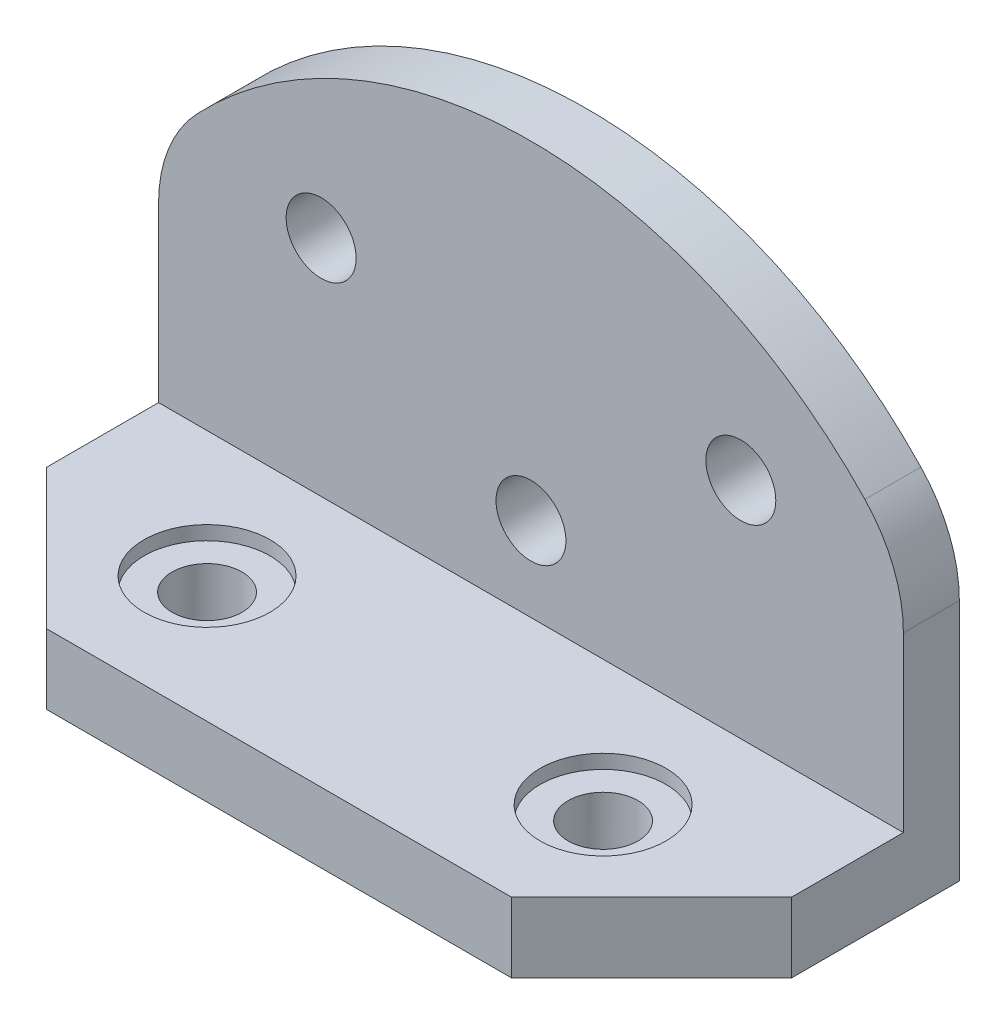
SolidWorks part; units mm, degrees
ref_plane "Front Plane" through (0, 0, 0) normal (0, 0, 1) x (1, 0, 0)
ref_plane "Top Plane" through (0, 0, 0) normal (0, 1, 0) x (1, 0, 0)
ref_plane "Right Plane" through (0, 0, 0) normal (1, 0, 0) x (0, 0, -1)
sketch "Sketch1" plane through (0, 0, 0) normal (0, 0, 1) x (1, 0, 0)
  line L0 (-7.5003, 10.7252) -> (7.4997, 10.7252) construction
  line L1 (-13.3097, 0.2252) -> (13.3097, 0.2252)
  line L2 (13.3097, 0.2252) -> (13.3097, 8.9074)
  line L3 (-13.3097, 8.9074) -> (-13.3097, 0.2252)
  line L4 (-0.0003, 5.7252) -> (-0.0003, 10.7252) construction
  arc A0 (13.3097, 8.9074) -> (11.935, 12.3509) centre (8.3097, 8.9074) ccw
  arc A1 (11.935, 12.3509) -> (-11.935, 12.3509) centre (0, 1.0143) ccw
  arc A2 (-11.935, 12.3509) -> (-13.3097, 8.9074) centre (-8.3097, 8.9074) ccw
  circle A3 centre (7.4997, 10.7252) radius 1.25
  circle A4 centre (-7.5003, 10.7252) radius 1.25
  circle A5 centre (-0.0003, 5.7252) radius 1.25
  dimension "D1" = 2.5
  dimension "D2" = 15
  dimension "D3" = 5
  dimension "D4" = 5.5
  dimension "D5" = 13.31
extrude "Boss-Extrude1" add sketch "Sketch1" along normal blind 2
sketch "Sketch2" plane through (0, 0, 2) normal (0, 0, 1) x (1, 0, 0)
  line L0 (13.3097, 0.2252) -> (13.3097, 8.9074) construction
  line L1 (-13.3097, 0.2252) -> (13.3097, 0.2252)
  line L2 (-13.3097, 0.2252) -> (-13.3097, 2.7252)
  line L3 (-13.3097, 2.7252) -> (13.3097, 2.7252)
  line L4 (13.3097, 0.2252) -> (13.3097, 2.7252)
  dimension "D1" = 2.5
extrude "Boss-Extrude2" add sketch "Sketch2" along normal blind 9
sketch "Sketch3" plane through (0, 2.7252, 0) normal (0, 1, 0) x (1, 0, 0)
  line L0 (-7.0774, -6.5) -> (7.0774, -6.5)
  line L1 (0, -6.5) -> (0, 0)
  line L2 (13.3097, -11) -> (-13.3097, -11) construction
  circle A0 centre (-7.0774, -6.5) radius 1.25
  circle A1 centre (7.0774, -6.5) radius 1.25
  dimension "D1" = 2.5
  dimension "D2" = 4.5
extrude "Cut-Extrude1" cut sketch "Sketch3" against normal blind 9
sketch "Sketch4" plane through (0, 2.7252, 0) normal (0, 1, 0) x (1, 0, 0)
  circle A2 centre (-7.0774, -6.5) radius 2.25
  circle A3 centre (7.0774, -6.5) radius 2.25
  dimension "D1" = 4.5
extrude "Cut-Extrude2" cut sketch "Sketch4" against normal blind 0.5
chamfer "Chamfer1" distance 5 angle 45 2 edges at (13.3097, 1.4752, 11) (-13.3097, 1.4752, 11)
